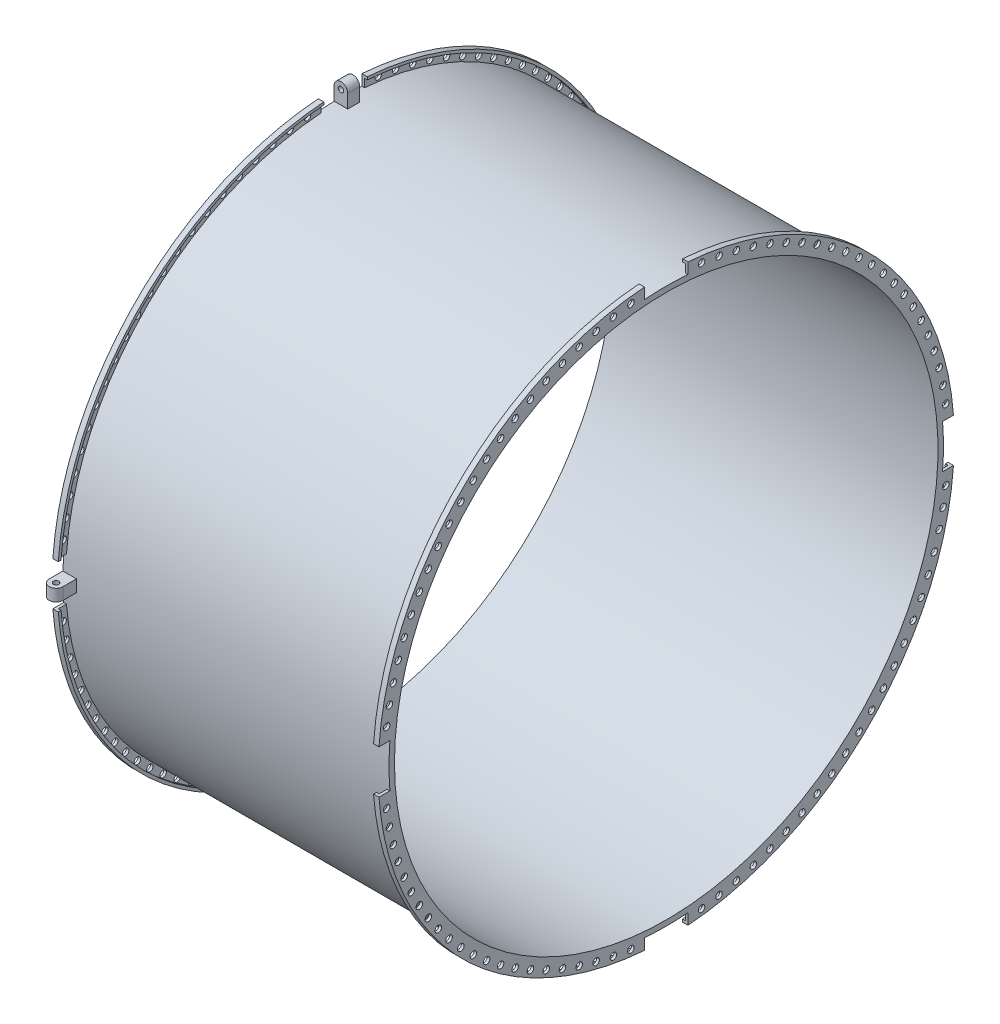
SolidWorks part; units mm, degrees
material "1.4122 (X39CrMo17-1)"
ref_plane "Ön Düzlem" through (0, 0, 0) normal (0, 0, 1) x (1, 0, 0)
ref_plane "Üst Düzlem" through (0, 0, 0) normal (0, 1, 0) x (1, 0, 0)
ref_plane "Sağ Düzlem" through (0, 0, 0) normal (1, 0, 0) x (0, 0, -1)
sketch "Çizim1" plane through (0, 0, 0) normal (0, 0, 1) x (1, 0, 0)
  line L0 (0, 0) -> (0, 30)
  line L1 (0, 30) -> (10, 30)
  line L2 (10, 30) -> (10, 25)
  line L3 (10, 25) -> (5, 25)
  line L4 (5, 25) -> (5, 10)
  line L5 (0, 0) -> (600, 0)
  line L6 (600, 0) -> (600, 30)
  line L7 (600, 30) -> (590, 30)
  line L8 (590, 30) -> (590, 25)
  line L9 (590, 25) -> (595, 25)
  line L10 (595, 25) -> (595, 10)
  line L11 (5, 10) -> (595, 10)
  dimension "D1" = 30
  dimension "D2" = 10
  dimension "D3" = 5
  dimension "D4" = 5
  dimension "D5" = 600
  dimension "D6" = 30
  dimension "D7" = 10
  dimension "D8" = 5
  dimension "D9" = 5
  dimension "D10" = 10
  dimension "D11" = 10
ref_plane "Düzlem1" through (0, -500, 0) normal (0, 1, 0) x (-1, 0, 0)
sketch "Çizim2" plane through (0, -500, 0) normal (0, 1, 0) x (-1, 0, 0)
  line L0 (0, 0) -> (-528.9975, 0) construction
revolve "Döndür1" add sketch "Çizim1" angle 360 about L0
sketch "Çizim3" plane through (0, 0, 0) normal (-1, 0, 0) x (0, 0, 1)
  line L0 (-40, 8.429) -> (-40, 28.4884)
  line L1 (40, 8.429) -> (40, 28.4884)
  line L2 (-40, -1008.429) -> (-40, -1028.4884)
  line L3 (40, -1008.429) -> (40, -1028.4884)
  line L4 (-528.4884, -540) -> (-508.429, -540)
  line L5 (-528.4884, -460) -> (-508.429, -460)
  line L6 (508.429, -460) -> (528.4884, -460)
  line L7 (508.429, -540) -> (528.4884, -540)
  circle A0 centre (0, -500) radius 510
  circle A1 centre (0, -500) radius 530 construction
  circle A2 centre (0, -500) radius 530
  point P19 (-510, -500)
  circle M2 centre (0, -500) radius 530
  dimension "D1" = 1020
  dimension "D4" = 1060
  dimension "D2" = 40
  dimension "D3" = 40
  dimension "D5" = 40
  dimension "D6" = 40
extrude "Kes-Ekstrüzyon1" cut sketch "Çizim3" against normal up to surface (600 mm away) contours A0 L1 L0 M2 | A0 L5 L4 M2 | A0 L2 L3 M2 | A0 L7 L6 M2 up to face at (600, -500, 530)
sketch "Çizim4" plane through (0, 0, 0) normal (-1, 0, 0) x (0, 0, 1)
  circle A0 centre (0, 18.4587) radius 6
  circle A1 centre (32.5543, 17.4356) radius 6
  circle A2 centre (64.9801, 14.3705) radius 6
  circle A3 centre (97.1495, 9.2754) radius 6
  circle A4 centre (128.9354, 2.1703) radius 6
  circle A5 centre (160.2125, -6.9165) radius 6
  circle A6 centre (190.8574, -17.9493) radius 6
  circle A7 centre (220.749, -30.8846) radius 6
  circle A8 centre (249.7694, -45.6712) radius 6
  circle A9 centre (277.8041, -62.2509) radius 6
  circle A10 centre (304.7424, -80.5581) radius 6
  circle A11 centre (330.478, -100.5207) radius 6
  circle A12 centre (354.9094, -122.0599) radius 6
  circle A13 centre (377.9401, -145.0906) radius 6
  circle A14 centre (399.4793, -169.522) radius 6
  circle A15 centre (419.4419, -195.2576) radius 6
  circle A16 centre (437.7491, -222.1959) radius 6
  circle A17 centre (454.3288, -250.2306) radius 6
  circle A18 centre (469.1154, -279.251) radius 6
  circle A19 centre (482.0507, -309.1426) radius 6
  circle A20 centre (493.0835, -339.7875) radius 6
  circle A21 centre (502.1703, -371.0646) radius 6
  circle A22 centre (509.2754, -402.8505) radius 6
  circle A23 centre (514.3705, -435.0199) radius 6
  circle A24 centre (517.4356, -467.4457) radius 6
  circle A25 centre (518.4587, -500) radius 6
  circle A26 centre (517.4356, -532.5543) radius 6
  circle A27 centre (514.3705, -564.9801) radius 6
  circle A28 centre (509.2754, -597.1495) radius 6
  circle A29 centre (502.1703, -628.9354) radius 6
  circle A30 centre (493.0835, -660.2125) radius 6
  circle A31 centre (482.0507, -690.8574) radius 6
  circle A32 centre (469.1154, -720.749) radius 6
  circle A33 centre (454.3288, -749.7694) radius 6
  circle A34 centre (437.7491, -777.8041) radius 6
  circle A35 centre (419.4419, -804.7424) radius 6
  circle A36 centre (399.4793, -830.478) radius 6
  circle A37 centre (377.9401, -854.9094) radius 6
  circle A38 centre (354.9094, -877.9401) radius 6
  circle A39 centre (330.478, -899.4793) radius 6
  circle A40 centre (304.7424, -919.4419) radius 6
  circle A41 centre (277.8041, -937.7491) radius 6
  circle A42 centre (249.7694, -954.3288) radius 6
  circle A43 centre (220.749, -969.1154) radius 6
  circle A44 centre (190.8574, -982.0507) radius 6
  circle A45 centre (160.2125, -993.0835) radius 6
  circle A46 centre (128.9354, -1002.1703) radius 6
  circle A47 centre (97.1495, -1009.2754) radius 6
  circle A48 centre (64.9801, -1014.3705) radius 6
  circle A49 centre (32.5543, -1017.4356) radius 6
  circle A50 centre (0, -1018.4587) radius 6
  circle A51 centre (-32.5543, -1017.4356) radius 6
  circle A52 centre (-64.9801, -1014.3705) radius 6
  circle A53 centre (-97.1495, -1009.2754) radius 6
  circle A54 centre (-128.9354, -1002.1703) radius 6
  circle A55 centre (-160.2125, -993.0835) radius 6
  circle A56 centre (-190.8574, -982.0507) radius 6
  circle A57 centre (-220.749, -969.1154) radius 6
  circle A58 centre (-249.7694, -954.3288) radius 6
  circle A59 centre (-277.8041, -937.7491) radius 6
  circle A60 centre (-304.7424, -919.4419) radius 6
  circle A61 centre (-330.478, -899.4793) radius 6
  circle A62 centre (-354.9094, -877.9401) radius 6
  circle A63 centre (-377.9401, -854.9094) radius 6
  circle A64 centre (-399.4793, -830.478) radius 6
  circle A65 centre (-419.4419, -804.7424) radius 6
  circle A66 centre (-437.7491, -777.8041) radius 6
  circle A67 centre (-454.3288, -749.7694) radius 6
  circle A68 centre (-469.1154, -720.749) radius 6
  circle A69 centre (-482.0507, -690.8574) radius 6
  circle A70 centre (-493.0835, -660.2125) radius 6
  circle A71 centre (-502.1703, -628.9354) radius 6
  circle A72 centre (-509.2754, -597.1495) radius 6
  circle A73 centre (-514.3705, -564.9801) radius 6
  circle A74 centre (-517.4356, -532.5543) radius 6
  circle A75 centre (-518.4587, -500) radius 6
  circle A76 centre (-517.4356, -467.4457) radius 6
  circle A77 centre (-514.3705, -435.0199) radius 6
  circle A78 centre (-509.2754, -402.8505) radius 6
  circle A79 centre (-502.1703, -371.0646) radius 6
  circle A80 centre (-493.0835, -339.7875) radius 6
  circle A81 centre (-482.0507, -309.1426) radius 6
  circle A82 centre (-469.1154, -279.251) radius 6
  circle A83 centre (-454.3288, -250.2306) radius 6
  circle A84 centre (-437.7491, -222.1959) radius 6
  circle A85 centre (-419.4419, -195.2576) radius 6
  circle A86 centre (-399.4793, -169.522) radius 6
  circle A87 centre (-377.9401, -145.0906) radius 6
  circle A88 centre (-354.9094, -122.0599) radius 6
  circle A89 centre (-330.478, -100.5207) radius 6
  circle A90 centre (-304.7424, -80.5581) radius 6
  circle A91 centre (-277.8041, -62.2509) radius 6
  circle A92 centre (-249.7694, -45.6712) radius 6
  circle A93 centre (-220.749, -30.8846) radius 6
  circle A94 centre (-190.8574, -17.9493) radius 6
  circle A95 centre (-160.2125, -6.9165) radius 6
  circle A96 centre (-128.9354, 2.1703) radius 6
  circle A97 centre (-97.1495, 9.2754) radius 6
  circle A98 centre (-64.9801, 14.3705) radius 6
  circle A99 centre (-32.5543, 17.4356) radius 6
  dimension "D1" = 12
  dimension "D2" = 100
extrude "Kes-Ekstrüzyon2" cut sketch "Çizim4" against normal up to surface (600 mm away) up to face at (600, -500, 500)
sketch "Çizim5" plane through (0, 0, 0) normal (0, 0, 1) x (1, 0, 0)
  line L0 (25, 10) -> (0, 10)
  line L1 (600, 10) -> (0, 10) construction
  line L3 (0, 10) -> (0, 35)
  line L4 (25, 10) -> (25, 35)
  arc A0 (25, 35) -> (0, 35) centre (12.5, 35) ccw
  circle A1 centre (12.5, 35) radius 5
  dimension "D4" = 25
  dimension "D5" = 10
  dimension "D1" = 25
  dimension "D2" = 25
  dimension "D3" = 25
extrude "Yükseklik-Ekstrüzyon1" add sketch "Çizim5" along normal mid plane 22 separate body
pattern_circular "Dairesel Çoğaltma11" count 4 over 360 about axis through (0, -500, 0) along (1, 0, 0) of bodies 104
ref_plane "Düzlem2" through (300, 0, 0) normal (1, 0, 0) x (0, 0, -1)
